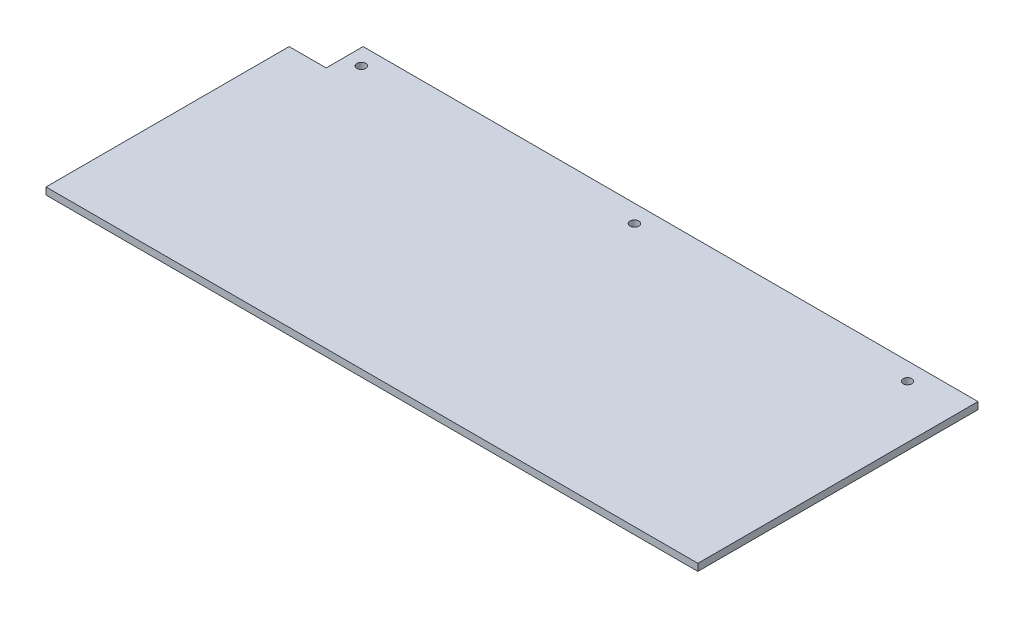
SolidWorks part; units mm, degrees
ref_plane "Front Plane" through (0, 0, 0) normal (0, 0, 1) x (1, 0, 0)
ref_plane "Top Plane" through (0, 0, 0) normal (0, 1, 0) x (1, 0, 0)
ref_plane "Right Plane" through (0, 0, 0) normal (1, 0, 0) x (0, 0, -1)
sketch "Sketch1" plane through (0, 0, 0) normal (0, 1, 0) x (1, 0, 0)
  line L0 (0, 90) -> (0, -90) construction
  line L1 (-185, -90) -> (185, -90) construction
  line L2 (-185, -90) -> (-185, 90) construction
  line L3 (-185, 90) -> (185, 90) construction
  line L4 (185, -90) -> (185, 90) construction
  line L5 (-185, -90) -> (185, 90) construction
  line L6 (-185, 90) -> (185, -90) construction
  line L7 (-185, 0) -> (185, 0) construction
  line L8 (-185, -69) -> (-185, 69)
  line L9 (-185, 90) -> (-164, 90) construction
  line L10 (-185, 90) -> (-185, 69) construction
  line L11 (-185, 69) -> (-164, 69)
  line L12 (-164, 90) -> (-164, 69)
  line L13 (-185, -90) -> (-164, -90) construction
  line L14 (-185, -90) -> (-185, -69) construction
  line L15 (-185, -69) -> (-164, -69)
  line L16 (-164, -90) -> (-164, -69) construction
  line L17 (-164, 90) -> (185, 90)
  line L18 (-164, -90) -> (185, -90) construction
  line L19 (-164, -69) -> (185, -69)
  line L20 (185, 90) -> (185, -69)
  circle A0 centre (-155, 80) radius 2.5
  circle A1 centre (0, 80) radius 2.5
  circle A2 centre (155, 80) radius 2.5
  circle A3 centre (-155, -80) radius 2.5 construction
  circle A4 centre (0, -80) radius 2.5 construction
  circle A5 centre (155, -80) radius 2.5 construction
  point P0 (0, 0)
  dimension "D3" = 5
  dimension "D4" = 5
  dimension "D7" = 30
  dimension "D8" = 21
  dimension "D1" = 180
  dimension "D2" = 370
  dimension "D5" = 10
  dimension "D6" = 10
  dimension "D9" = 21
  dimension "D10" = 21
  dimension "D11" = 21
extrude "Boss-Extrude1" add sketch "Sketch1" along normal blind 4
